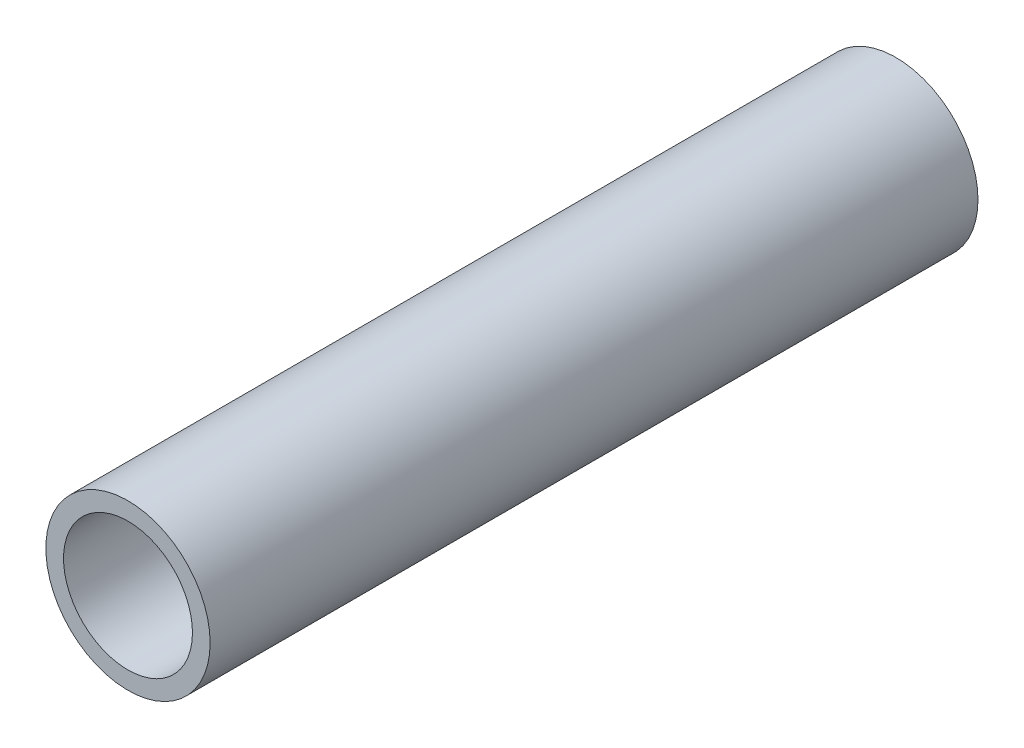
SolidWorks part; units mm, degrees
material "PVC 0.007 Plasticized"
ref_plane "Front Plane" through (0, 0, 0) normal (0, 0, 1) x (1, 0, 0)
ref_plane "Top Plane" through (0, 0, 0) normal (0, 1, 0) x (1, 0, 0)
ref_plane "Right Plane" through (0, 0, 0) normal (1, 0, 0) x (0, 0, -1)
sketch "Sketch1" plane through (0, 0, 0) normal (0, 0, 1) x (1, 0, 0)
  line L0 (10.4648, 0) -> (13.335, 0) construction
  circle A0 centre (0, 0) radius 13.335 construction
  circle A1 centre (0, 0) radius 10.4648 construction
  dimension "ID" = 20.9296
  dimension "OD" = 26.67
  dimension "Wall Thickness" = 2.8702
sketch "Sketch2" plane through (0, 0, 0) normal (1, 0, 0) x (0, 0, -1)
  line L0 (-762, 0) -> (762, 0) construction
  line L1 (-728.6625, 13.335) -> (-728.6625, -13.335) construction
  line L2 (728.6625, 13.335) -> (728.6625, -13.335) construction
  point P4 (0, 0)
  point P8 (-728.6625, 0)
  point P11 (728.6625, 0)
  dimension "Length" = 1524
  dimension "D1" = 33.3375
  dimension "D2" = 33.3375
  dimension "D3" = 26.67
sketch "Sketch3" plane through (0, 0, 0) normal (0, 0, 1) x (1, 0, 0)
  circle A0 centre (0, 0) radius 13.335
  circle A1 centre (0, 0) radius 13.335 construction
  circle A2 centre (0, 0) radius 10.4648 construction
  circle A3 centre (0, 0) radius 10.4648
extrude "Boss-Extrude1" add sketch "Sketch3" along normal up to vertex (762 mm away) and the other way up to vertex (762 mm away) up to point (0, 0, 762) other way up to point (0, 0, -762)
sketch "Sketch4" plane through (0, 0, 762) normal (0, 0, 1) x (1, 0, 0)
  circle A0 centre (0, 0) radius 10.4648 construction
  circle A1 centre (0, 0) radius 13.335 construction
  circle A2 centre (0, 0) radius 10.4648
  circle A3 centre (0, 0) radius 13.335
extrude "Cut-Extrude2" cut sketch "Sketch4" against normal offset from surface (1399.3555 mm away) 124.6445 contours A3 up to face at (10.4648, 0, -762)
equation "\"D1@Sketch2\"=\"OD@Sketch1\" * 1.25"
equation "\"D2@Sketch2\"=\"D1@Sketch2\""
equation "\"D3@Sketch2\"= \"OD@Sketch1\""
